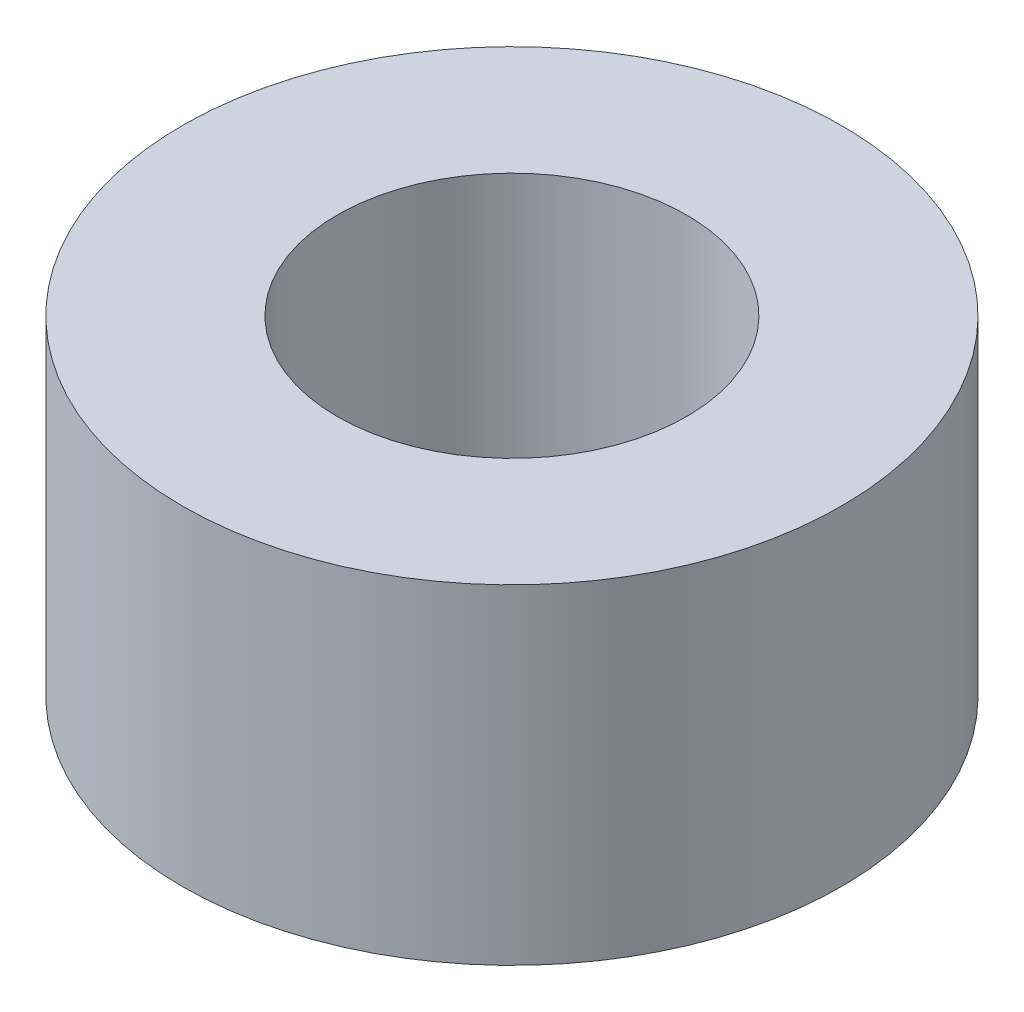
SolidWorks part; units mm, degrees
ref_plane "Front Plane" through (0, 0, 0) normal (0, 0, 1) x (1, 0, 0)
ref_plane "Top Plane" through (0, 0, 0) normal (0, 1, 0) x (1, 0, 0)
ref_plane "Right Plane" through (0, 0, 0) normal (1, 0, 0) x (0, 0, -1)
sketch "Sketch1" plane through (0, 0, 0) normal (0, 1, 0) x (1, 0, 0)
  circle A0 centre (0, 0) radius 2.65
  circle A1 centre (0, 0) radius 5
  dimension "D1" = 5.3
  dimension "D2" = 10
extrude "Boss-Extrude1" add sketch "Sketch1" along normal blind 5
